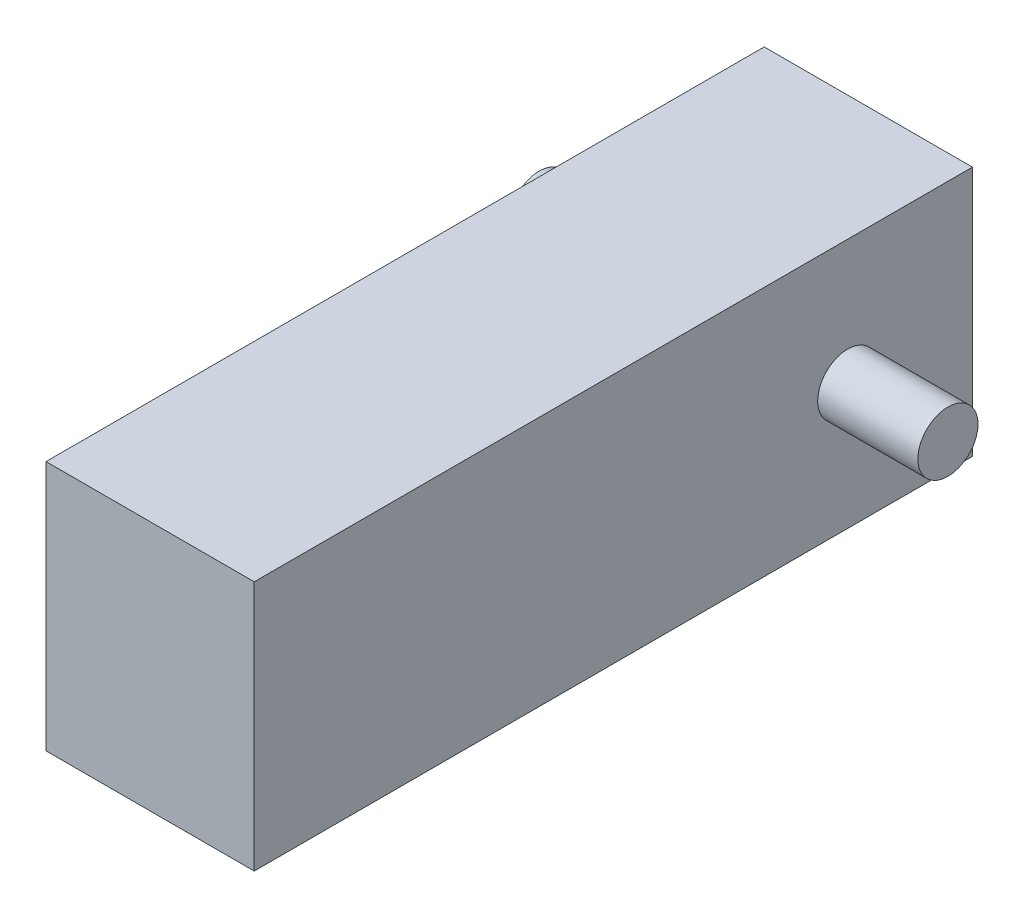
SolidWorks part; units mm, degrees
ref_plane "Front Plane" through (0, 0, 0) normal (0, 0, 1) x (1, 0, 0)
ref_plane "Top Plane" through (0, 0, 0) normal (0, 1, 0) x (1, 0, 0)
ref_plane "Right Plane" through (0, 0, 0) normal (1, 0, 0) x (0, 0, -1)
sketch "Sketch1" plane through (0, 0, 0) normal (0, 1, 0) x (1, 0, 0)
  line L1 (-9.35, -32.25) -> (9.35, -32.25)
  line L2 (-9.35, -32.25) -> (-9.35, 32.25)
  line L3 (-9.35, 32.25) -> (9.35, 32.25)
  line L4 (9.35, -32.25) -> (9.35, 32.25)
  line L5 (-9.35, -32.25) -> (9.35, 32.25) construction
  line L6 (-9.35, 32.25) -> (9.35, -32.25) construction
  point P0 (0, 0)
  dimension "D1" = 18.7
  dimension "D2" = 64.5
extrude "Boss-Extrude1" add sketch "Sketch1" along normal blind 22.5
sketch "Sketch2" plane through (9.35, 0, 0) normal (1, 0, 0) x (0, 0, -1)
  line L0 (32.25, 11.25) -> (21.05, 11.25) construction
  line L1 (32.25, 22.5) -> (32.25, 0) construction
  circle A0 centre (21.05, 11.25) radius 2.7
  dimension "D2" = 5.4
  dimension "D1" = 11.2
extrude "Boss-Extrude2" add sketch "Sketch2" along normal blind 9
sketch "Sketch3" plane through (0, 22.5, 0) normal (0, 1, 0) x (1, 0, 0)
  line L0 (0, 32.25) -> (0, -32.25) construction
  line L1 (9.35, 32.25) -> (-9.35, 32.25) construction
  line L2 (-9.35, -32.25) -> (9.35, -32.25) construction
  line L3 (18.35, 21.05) -> (-18.35, 21.05) construction
  line L4 (18.35, 18.35) -> (18.35, 23.75) construction
  dimension "D1" = 36.7
mirror "Mirror1" about plane through (0, 0, 0) normal (1, 0, 0) of "Boss-Extrude2"
